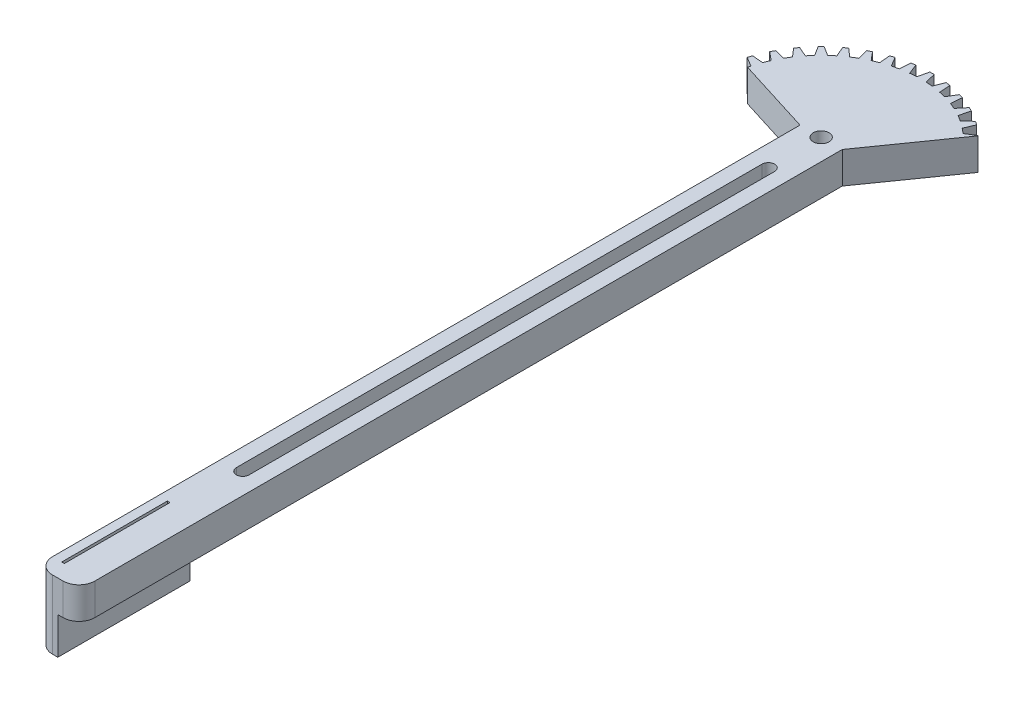
SolidWorks part; units mm, degrees
material "PBT General Purpose"
ref_plane "Front Plane" through (0, 0, 0) normal (0, 0, 1) x (1, 0, 0)
ref_plane "Top Plane" through (0, 0, 0) normal (0, 1, 0) x (1, 0, 0)
ref_plane "Right Plane" through (0, 0, 0) normal (1, 0, 0) x (0, 0, -1)
sketch "Sketch1" plane through (0, 0, 0) normal (0, 1, 0) x (1, 0, 0)
  circle A0 centre (0, 0) radius 21
  circle A1 centre (0, 0) radius 1.5
  dimension "D2" = 3
  dimension "D1" = 42
extrude "Boss-Extrude1" add sketch "Sketch1" along normal blind 6
sketch "Sketch2" plane through (0, 6, 0) normal (0, 1, 0) x (1, 0, 0)
  line L0 (0, 0) -> (0, 15.5) construction
  line L1 (0, 0) -> (-0.4123, 20.996) construction
  line L2 (0, 0) -> (-0.8702, 18.9801) construction
  line L3 (0, 0) -> (-1.4907, 18.9414) construction
  line L4 (-0.8702, 18.9801) -> (-0.4123, 20.996)
  line L5 (0.8702, 18.9801) -> (0.4123, 20.996)
  line L6 (-1.4907, 18.9414) -> (-1.7314, 22)
  line L7 (1.4907, 18.9414) -> (1.7314, 22)
  line L8 (-1.7314, 22) -> (1.7314, 22)
  arc A0 (-0.8702, 18.9801) -> (-1.4907, 18.9414) centre (0, 0) ccw
  circle A1 centre (0, 0) radius 21 construction
  arc A2 (0.4123, 20.996) -> (-0.4123, 20.996) centre (0, 0) ccw
  arc A3 (0.8702, 18.9801) -> (1.4907, 18.9414) centre (0, 0) cw
  dimension "D1" = 19
  dimension "D2" = 1.125
  dimension "D3" = 1.5
  dimension "D4" = 1.875
  dimension "D5" = 22
extrude "Cut-Extrude1" cut sketch "Sketch2" against normal up to next (6 mm away)
pattern_circular "CirPattern1" count 40 over 360 about axis through (0, 0, 0) along (0, 1, 0) of "Cut-Extrude1"
sketch "Sketch3" plane through (0, 6, 0) normal (0, 1, 0) x (1, 0, 0)
  line L0 (4, 0) -> (-4, 0) construction
  line L1 (0, 0) -> (0, 21.0096) construction
  line L2 (0, 0) -> (-26.0972, 6.5552) construction
  line L3 (-4, 0) -> (-20.3673, 5.1159)
  line L4 (-4, 0) -> (4, 0)
  line L6 (0, 0) -> (-7.8504, 27.559) construction
  line L7 (0, 0) -> (15.7913, 16.2954) construction
  line L8 (4, 0) -> (14.6142, 15.0807)
  arc A0 (-20.3673, 5.1159) -> (14.6142, 15.0807) centre (0, 0) ccw
  point P5 (0, 0)
  dimension "D3" = 21
  dimension "D1" = 8
  dimension "D2" = 60
  dimension "D4" = 15.9
  dimension "D5" = 120
extrude "Cut-Extrude2" cut sketch "Sketch3" against normal up to next
sketch "Sketch4" plane through (0, 0, 0) normal (0, -1, 0) x (1, 0, 0)
  line L0 (1.5, 0) -> (4, 0)
  line L1 (-4, 0) -> (-1.5, 0)
  line L2 (-4, 0) -> (-4, 141.5)
  line L3 (-1, 144.5) -> (1, 144.5)
  line L4 (4, 0) -> (4, 141.5)
  arc A0 (1.5, 0) -> (-1.5, 0) centre (0, 0) ccw
  arc A1 (-4, 141.5) -> (-1, 144.5) centre (-1, 141.5) cw
  arc A2 (1, 144.5) -> (4, 141.5) centre (1, 141.5) cw
  point P5 (0, 140)
  point P12 (0, 140)
  point P14 (0, 140)
  dimension "D5" = 3
  dimension "D1" = 4.5
  dimension "D3" = 140
extrude "Boss-Extrude2" add sketch "Sketch4" against normal up to surface (6 mm away) up to face at (-4.0836, 6, -14.6127)
sketch "Sketch5" plane through (0, 0, 0) normal (0, -1, 0) x (1, 0, 0)
  line L0 (-4, 119.5) -> (4, 119.5)
  line L1 (0, 119.5) -> (0, 144.5)
  line L32 (14.6142, -15.0807) -> (4, 0)
  line L33 (4, 0) -> (4, 141.5)
  line L34 (4, 0) -> (4, 141.5)
  line L35 (1, 144.5) -> (-1, 144.5)
  line L36 (-4, 0) -> (-18.455, -4.5182)
  line L37 (-18.32, -5.0376) -> (-20.0957, -6.096)
  line L38 (-19.8409, -6.8802) -> (-17.7822, -6.6928)
  line L39 (-17.3064, -7.8414) -> (-18.8947, -9.1646)
  line L40 (-18.5203, -9.8993) -> (-16.5163, -9.3921)
  line L41 (-15.8667, -10.4522) -> (-17.2284, -12.0075)
  line L42 (-16.7437, -12.6747) -> (-14.8437, -11.8602)
  line L43 (-14.0362, -12.8056) -> (-15.1379, -14.5548)
  line L44 (-14.5548, -15.1379) -> (-12.8056, -14.0362)
  line L45 (-11.8602, -14.8437) -> (-12.6747, -16.7437)
  line L46 (-12.0075, -17.2284) -> (-10.4522, -15.8667)
  line L47 (-9.3921, -16.5163) -> (-9.8993, -18.5203)
  line L48 (-9.1646, -18.8947) -> (-7.8414, -17.3064)
  line L49 (-6.6928, -17.7822) -> (-6.8802, -19.8409)
  line L50 (-6.096, -20.0957) -> (-5.0376, -18.32)
  line L51 (-3.8286, -18.6103) -> (-3.6917, -20.673)
  line L52 (-2.8773, -20.802) -> (-2.1097, -18.8825)
  line L53 (-0.8702, -18.9801) -> (-0.4123, -20.996)
  line L54 (0.4123, -20.996) -> (0.8702, -18.9801)
  line L55 (2.1097, -18.8825) -> (2.8773, -20.802)
  line L56 (3.6917, -20.673) -> (3.8286, -18.6103)
  line L57 (5.0376, -18.32) -> (6.096, -20.0957)
  line L58 (6.8802, -19.8409) -> (6.6928, -17.7822)
  line L59 (7.8414, -17.3064) -> (9.1646, -18.8947)
  line L60 (9.8993, -18.5203) -> (9.3921, -16.5163)
  line L61 (10.4522, -15.8667) -> (12.0075, -17.2284)
  line L62 (12.6747, -16.7437) -> (11.8602, -14.8437)
  line L63 (12.8056, -14.0362) -> (14.5548, -15.1379)
  line L97 (1, 144.5) -> (-1, 144.5)
  line L99 (-4, 141.5) -> (-4, 0)
  line L100 (-4, 141.5) -> (-4, 0)
  arc A28 (4, 141.5) -> (1, 144.5) centre (1, 141.5) ccw
  arc A29 (4, 141.5) -> (1, 144.5) centre (1, 141.5) ccw
  arc A31 (-20.0957, -6.096) -> (-19.8409, -6.8802) centre (0, 0) ccw
  arc A32 (-17.7822, -6.6928) -> (-17.3064, -7.8414) centre (0, 0) ccw
  arc A33 (-18.8947, -9.1646) -> (-18.5203, -9.8993) centre (0, 0) ccw
  arc A34 (-16.5163, -9.3921) -> (-15.8667, -10.4522) centre (0, 0) ccw
  arc A35 (-17.2284, -12.0075) -> (-16.7437, -12.6747) centre (0, 0) ccw
  arc A36 (-14.8437, -11.8602) -> (-14.0362, -12.8056) centre (0, 0) ccw
  arc A37 (-15.1379, -14.5548) -> (-14.5548, -15.1379) centre (0, 0) ccw
  arc A38 (-12.8056, -14.0362) -> (-11.8602, -14.8437) centre (0, 0) ccw
  arc A39 (-12.6747, -16.7437) -> (-12.0075, -17.2284) centre (0, 0) ccw
  arc A40 (-10.4522, -15.8667) -> (-9.3921, -16.5163) centre (0, 0) ccw
  arc A41 (-9.8993, -18.5203) -> (-9.1646, -18.8947) centre (0, 0) ccw
  arc A42 (-7.8414, -17.3064) -> (-6.6928, -17.7822) centre (0, 0) ccw
  arc A43 (-6.8802, -19.8409) -> (-6.096, -20.0957) centre (0, 0) ccw
  arc A44 (-5.0376, -18.32) -> (-3.8286, -18.6103) centre (0, 0) ccw
  arc A45 (-3.6917, -20.673) -> (-2.8773, -20.802) centre (0, 0) ccw
  arc A46 (-2.1097, -18.8825) -> (-0.8702, -18.9801) centre (0, 0) ccw
  arc A47 (-0.4123, -20.996) -> (0.4123, -20.996) centre (0, 0) ccw
  arc A48 (0.8702, -18.9801) -> (2.1097, -18.8825) centre (0, 0) ccw
  arc A49 (2.8773, -20.802) -> (3.6917, -20.673) centre (0, 0) ccw
  arc A50 (3.8286, -18.6103) -> (5.0376, -18.32) centre (0, 0) ccw
  arc A51 (6.096, -20.0957) -> (6.8802, -19.8409) centre (0, 0) ccw
  arc A52 (6.6928, -17.7822) -> (7.8414, -17.3064) centre (0, 0) ccw
  arc A53 (9.1646, -18.8947) -> (9.8993, -18.5203) centre (0, 0) ccw
  arc A54 (9.3921, -16.5163) -> (10.4522, -15.8667) centre (0, 0) ccw
  arc A55 (12.0075, -17.2284) -> (12.6747, -16.7437) centre (0, 0) ccw
  arc A56 (11.8602, -14.8437) -> (12.8056, -14.0362) centre (0, 0) ccw
  arc A57 (14.5548, -15.1379) -> (14.6142, -15.0807) centre (0, 0) ccw
  arc A87 (-1, 144.5) -> (-4, 141.5) centre (-1, 141.5) ccw
  arc A88 (-1, 144.5) -> (-4, 141.5) centre (-1, 141.5) ccw
  arc A90 (-18.455, -4.5182) -> (-18.32, -5.0376) centre (0, 0) ccw
  arc A91 (-18.455, -4.5182) -> (-18.32, -5.0376) centre (0, 0) ccw
  dimension "D2" = 25
  dimension "D1" = 0
extrude "Boss-Extrude3" add sketch "Sketch5" along normal blind 7 contours L97 A88 L100 L0 L1
sketch "Sketch7" plane through (0, -7, 0) normal (0, -1, 0) x (1, 0, 0)
  line L0 (-4, 119.5) -> (0, 119.5) construction
  line L1 (-2.25, 121.5) -> (-1.75, 121.5)
  line L2 (-2.25, 121.5) -> (-2.25, 141.5)
  line L3 (-2.25, 141.5) -> (-1.75, 141.5)
  line L4 (-1.75, 121.5) -> (-1.75, 141.5)
  point P6 (-2, 119.5)
  point P7 (-2, 121.5)
  dimension "D1" = 0.5
  dimension "D2" = 2
  dimension "D3" = 20
extrude "Cut-Extrude4" cut sketch "Sketch7" against normal up to next
sketch "Sketch8" plane through (0, 0, 0) normal (0, -1, 0) x (1, 0, 0)
  line L0 (0, 10) -> (0, 109.5) construction
  line L1 (-1.2, 10) -> (-1.2, 109.5)
  line L2 (1.2, 10) -> (1.2, 109.5)
  line L3 (-4, 119.5) -> (0, 119.5) construction
  arc A0 (-1.2, 10) -> (1.2, 10) centre (0, 10) ccw
  arc A1 (1.2, 109.5) -> (-1.2, 109.5) centre (0, 109.5) ccw
  point P3 (0, 59.75)
  dimension "D3" = 1.2
  dimension "D1" = 10
  dimension "D2" = 10
extrude "Cut-Extrude5" cut sketch "Sketch8" against normal up to next
equation "\"num_teeth\"= 40"
equation "\"D2@Sketch2\"=(1.5/6)*(360 / \"num_teeth\")*0.5"
equation "\"D3@Sketch2\"=(2/6)*(360 / \"num_teeth\")*0.5"
equation "\"D4@Sketch2\"=(2.5/6)*(360 / \"num_teeth\")*0.5"
equation "\"D1@CirPattern1\"=\"num_teeth\""
equation "\"teeth_angle_offset\"= 15.9deg"
equation "\"D4@Sketch3\"=\"teeth_angle_offset\""
equation "\"diameter\"= 40mm"
equation "\"D1@Sketch1\"=\"diameter\" + 2"
equation "\"D1@Sketch2\"=(\"diameter\" / 2) - 1"
equation "\"D3@Sketch3\"=(\"diameter\" / 2) + 1"
equation "\"teeth_fraction_required\"= 1 / 3"
equation "\"D5@Sketch3\"=360 * \"teeth_fraction_required\""
equation "\"D2@Sketch3\"=360 * \"teeth_fraction_required\" * 0.5"
equation "\"bar_length\"= 140mm"
equation "\"D3@Sketch4\"=\"bar_length\""
equation "\"D5@Sketch2\"=\"diameter\" / 2 + 2"
